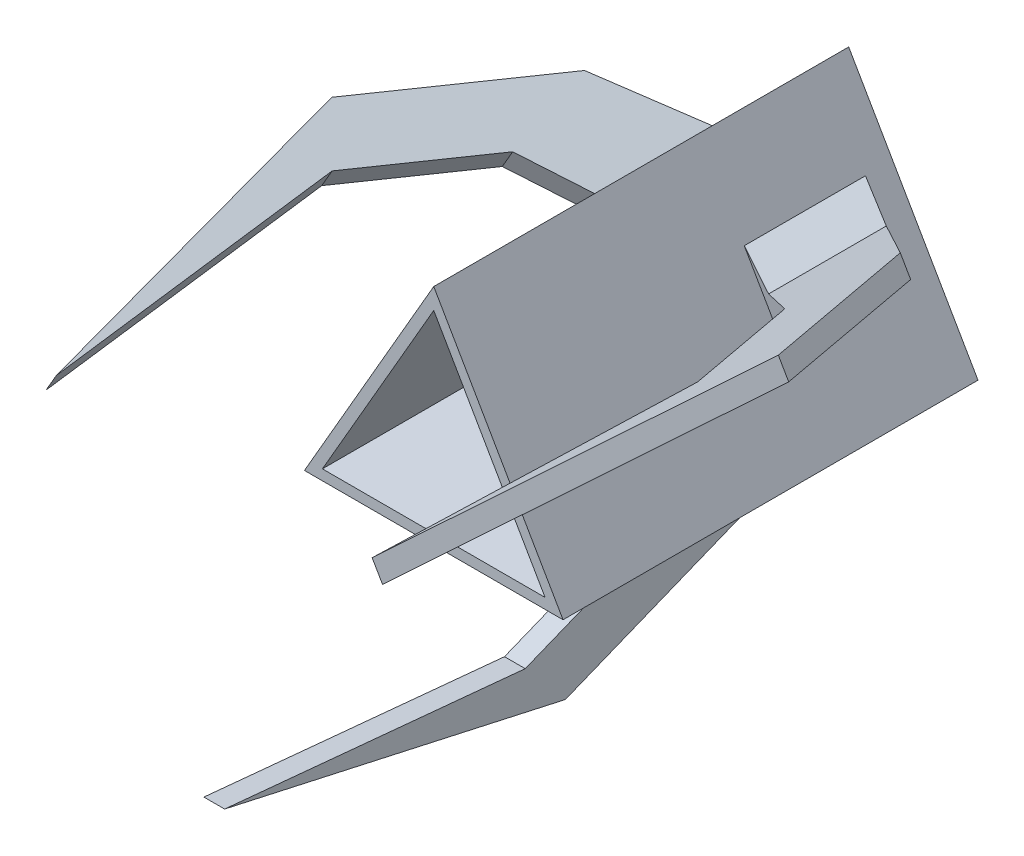
SolidWorks part; units mm, degrees
ref_plane "Front Plane" through (0, 0, 0) normal (0, 0, 1) x (1, 0, 0)
ref_plane "Top Plane" through (0, 0, 0) normal (0, 1, 0) x (1, 0, 0)
ref_plane "Right Plane" through (0, 0, 0) normal (1, 0, 0) x (0, 0, -1)
sketch "Sketch1" plane through (0, 0, 0) normal (0, 0, 1) x (1, 0, 0)
  line L1 (0, 10.3923) -> (-9, -5.1962)
  line L2 (-9, -5.1962) -> (9, -5.1962)
  line L3 (9, -5.1962) -> (0, 10.3923)
  line L4 (0, 14.3923) -> (-12.4641, -7.1962)
  line L5 (-12.4641, -7.1962) -> (12.4641, -7.1962)
  line L6 (12.4641, -7.1962) -> (0, 14.3923)
  circle A0 centre (0, 0) radius 5.1962 construction
  circle A1 centre (0, 0) radius 7.1962 construction
  dimension "D1" = 18
  dimension "D2" = 2
extrude "Boss-Extrude1" add sketch "Sketch1" along normal blind 10
sketch "Sketch2" plane through (0, 0, 10) normal (0, 0, 1) x (1, 0, 0)
  line L0 (-12.4641, -7.1962) -> (12.4641, -7.1962) construction
  line L2 (-4, 4.5) -> (4, 4.5)
  line L3 (-4, 4.5) -> (-4, -4.5)
  line L4 (-4, -4.5) -> (4, -4.5)
  line L5 (4, 4.5) -> (4, -4.5)
  line L6 (-4, 4.5) -> (4, -4.5) construction
  line L7 (-4, -4.5) -> (4, 4.5) construction
  line L8 (12.4641, -7.1962) -> (0, 14.3923) construction
  line L9 (-5.1681, -5.4409) -> (5.1681, -5.4409)
  line L10 (-5.1681, -5.4409) -> (-5.1681, 5.4409)
  line L11 (-5.1681, 5.4409) -> (5.1681, 5.4409)
  line L12 (5.1681, -5.4409) -> (5.1681, 5.4409)
  line L13 (-5.1681, -5.4409) -> (5.1681, 5.4409) construction
  line L14 (-5.1681, 5.4409) -> (5.1681, -5.4409) construction
  point P0 (0, 0)
  point P7 (0, -7.1962)
  point P9 (0, 0)
  dimension "D1" = 9
  dimension "D2" = 8
extrude "Boss-Extrude2" add sketch "Sketch2" against normal up to surface (10 mm away) up to face at (0, 0, 0)
sketch "Sketch3" plane through (0, 0, 10) normal (0, 0, 1) x (1, 0, 0)
  line L1 (0, 14.3923) -> (-12.4641, -7.1962)
  line L2 (-12.4641, -7.1962) -> (12.4641, -7.1962)
  line L3 (12.4641, -7.1962) -> (0, 14.3923)
  circle A0 centre (0, 0) radius 7.1962 construction
extrude "Extrude-Thin1" add sketch "Sketch3" along normal blind 30 thin thin type one direction reverse wall 1
ref_plane "Plane1" through (0, 0, 0) normal (-0.5, 0.866, 0) x (0.866, 0.5, 0)
sketch "Sketch4" plane through (0, 0, 0) normal (-0.5, 0.866, 0) x (0.866, 0.5, 0)
  line L0 (7.1962, 0) -> (7.1962, -40)
  line L1 (7.1962, -2.618) -> (7.1962, -14.2982)
  line L2 (7.1962, -2.618) -> (18.1515, -10.2475)
  line L3 (18.1515, -10.2475) -> (25.432, -28.309)
  line L4 (25.432, -28.309) -> (18.1515, -61.1568)
  line L5 (18.1515, -61.1568) -> (20.9192, -32.18)
  line L6 (20.9192, -32.18) -> (15.7186, -19.2783)
  line L7 (15.7186, -19.2783) -> (7.1962, -14.2982)
extrude "Boss-Extrude3" add sketch "Sketch4" along normal mid plane 2
mirror "Mirror1" about plane through (0, 0, 0) normal (1, 0, 0) of "Boss-Extrude3"
mirror "Mirror2" about plane through (0, 0, 0) normal (-0.5, 0.866, 0) of "Mirror1", "Boss-Extrude3"
chamfer "Chamfer2" distance 3 angle 45 6 edges at (5.7321, 4.4641, 8.4581) (-5.7321, 4.4641, 8.4581) (-6.7321, 2.7321, 8.4581) (-1, -7.1962, 8.4581) (6.7321, 2.7321, 8.4581) (1, -7.1962, 8.4581)
sketch "Sketch5" plane through (0, 0, 0) normal (0, 0, -1) x (-1, 0, 0)
  line L1 (0, 10.3923) -> (-9, -5.1962)
  line L2 (-9, -5.1962) -> (9, -5.1962)
  line L3 (9, -5.1962) -> (0, 10.3923)
  circle A0 centre (0, 0) radius 5.1962 construction
extrude "Cut-Extrude1" cut sketch "Sketch5" against normal blind 5
